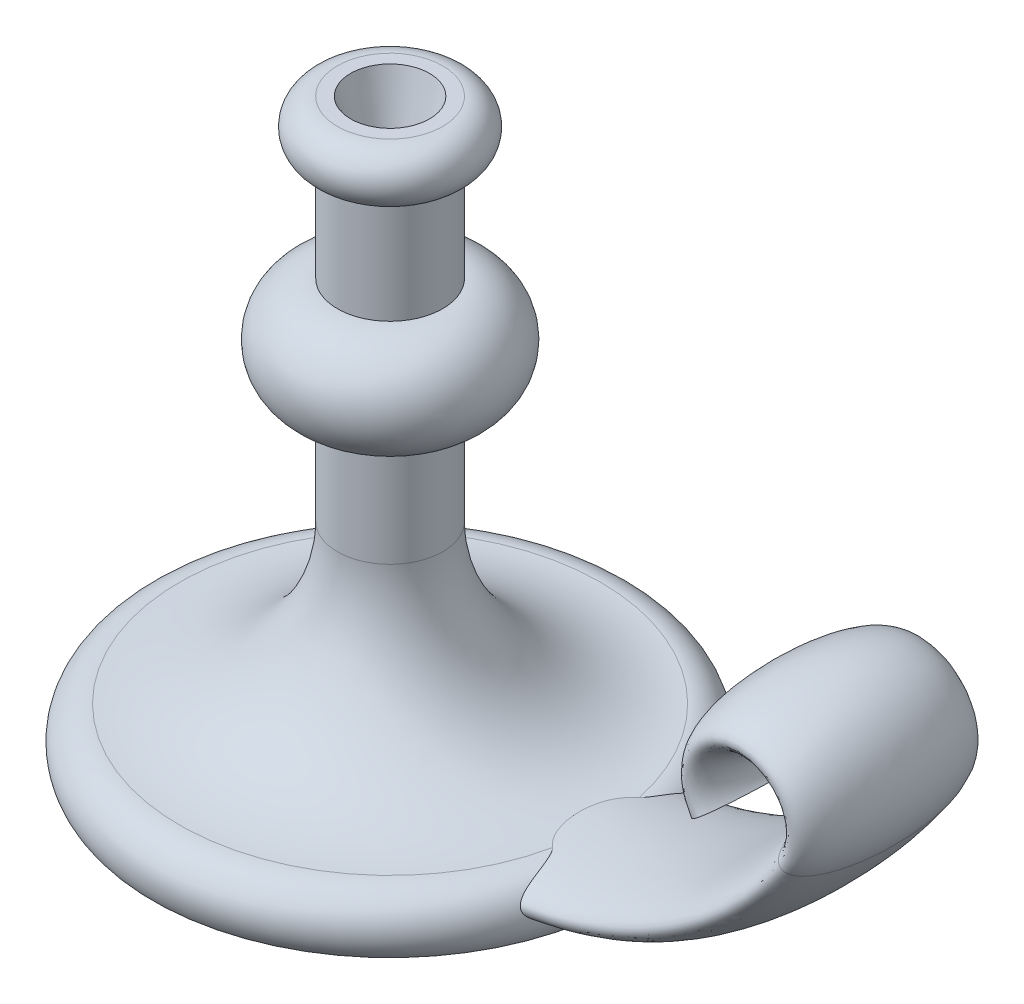
SolidWorks part; units mm, degrees
ref_plane "Front Plane" through (0, 0, 0) normal (0, 0, 1) x (1, 0, 0)
ref_plane "Top Plane" through (0, 0, 0) normal (0, 1, 0) x (1, 0, 0)
ref_plane "Right Plane" through (0, 0, 0) normal (1, 0, 0) x (0, 0, -1)
sketch "Sketch1" plane through (0, 0, 0) normal (0, 0, 1) x (1, 0, 0)
  line L0 (0, 0) -> (0, 220)
  line L1 (0, 220) -> (20, 220)
  line L2 (0, 0) -> (90, 0)
  line L3 (20, 200) -> (20, 160)
  line L4 (20, 120) -> (20, 80)
  arc A0 (20, 220) -> (20, 200) centre (20, 210) cw
  arc A1 (20, 160) -> (20, 120) centre (20, 140) cw
  arc A2 (20, 80) -> (80, 20) centre (80, 80) ccw
  arc A3 (80, 20) -> (90, 0) centre (80, 7.5) cw
  dimension "D4" = 10
  dimension "D6" = 20
  dimension "D5" = 60
  dimension "D9" = 12.5
  dimension "D1" = 220
  dimension "D2" = 90
  dimension "D3" = 20
  dimension "D7" = 40
  dimension "D8" = 80
revolve "Revolve1" add sketch "Sketch1" angle 360 about L0
sketch "Sketch2" plane through (0, 0, 0) normal (0, 0, 1) x (1, 0, 0)
  line L0 (0, 10) -> (60, 10)
  line L1 (0, 164) -> (0, 92) construction
  line L2 (-90, 0) -> (90, 0) construction
  arc A0 (60, 10) -> (183.5921, 75) centre (60, 160) ccw
  arc A1 (183.5921, 75) -> (150.6342, 75) centre (167.1131, 86.3333) ccw
  dimension "D1" = 65
  dimension "D2" = 150
  dimension "D3" = 20
  dimension "D4" = 60
  dimension "D5" = 10
sketch "Sketch3" plane through (0, 0, 0) normal (1, 0, 0) x (0, 0, -1)
  ellipse E0 centre (0, 10) end of major axis (35, 10) minor radius 10
sweep "Sweep2" add profiles "Sketch3" path "Sketch2"
sketch "Sketch6" plane through (0, 220, 0) normal (0, 1, 0) x (1, 0, 0)
  circle A0 centre (0, 0) radius 15
  dimension "D1" = 30
extrude "Cut-Extrude1" cut sketch "Sketch6" against normal blind 25 draft 15
